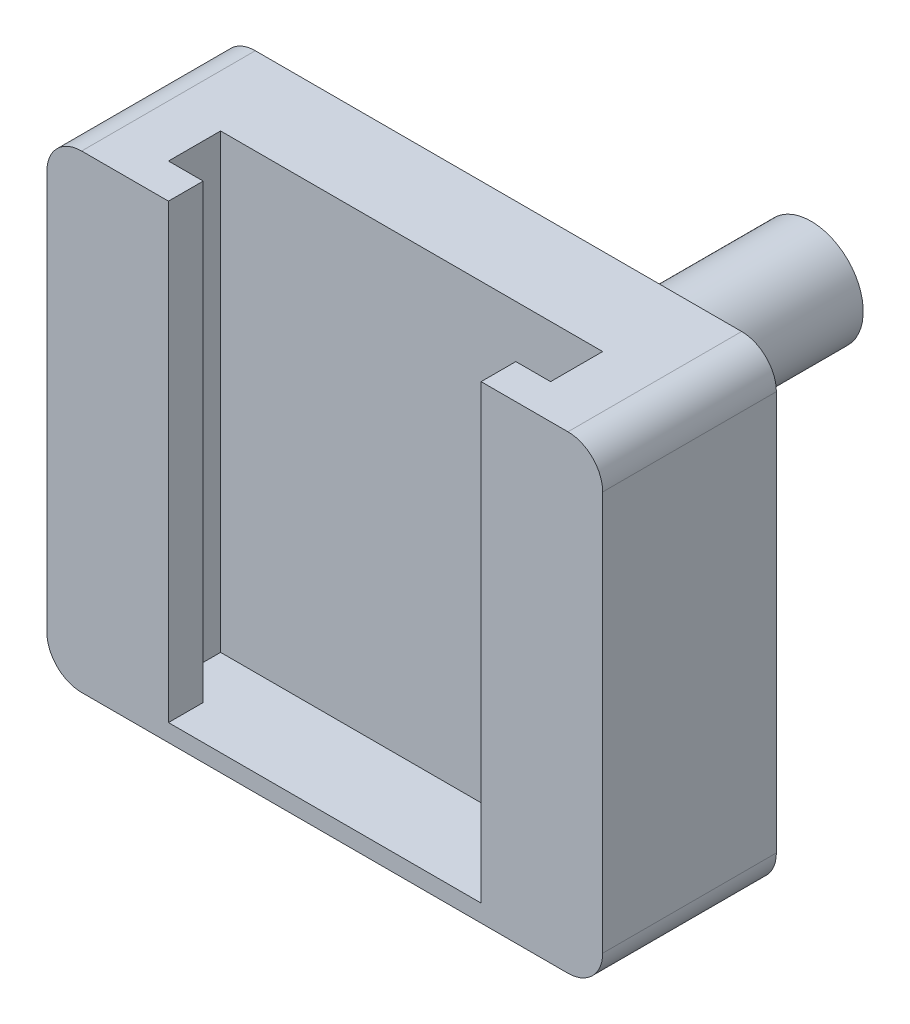
SolidWorks part; units mm, degrees
ref_plane "Front Plane" through (0, 0, 0) normal (0, 0, 1) x (1, 0, 0)
ref_plane "Top Plane" through (0, 0, 0) normal (0, 1, 0) x (1, 0, 0)
ref_plane "Right Plane" through (0, 0, 0) normal (1, 0, 0) x (0, 0, -1)
sketch "Sketch1" plane through (0, 0, 0) normal (0, 0, 1) x (1, 0, 0)
  line L1 (-16, -13.5) -> (16, -13.5)
  line L2 (-16, -13.5) -> (-16, 13.5)
  line L3 (-16, 13.5) -> (16, 13.5)
  line L4 (16, -13.5) -> (16, 13.5)
  line L5 (-16, -13.5) -> (16, 13.5) construction
  line L6 (-16, 13.5) -> (16, -13.5) construction
  point P0 (0, 0)
  dimension "D1" = 32
  dimension "D2" = 27
extrude "Boss-Extrude1" add sketch "Sketch1" along normal blind 10 contours L3 L4 L1 L2
fillet "Fillet1" radius 2 4 edges at (16, 13.5, 5) (-16, 13.5, 5) (16, -13.5, 5) (-16, -13.5, 5)
sketch "Sketch2" plane through (0, 13.5, 0) normal (0, 1, 0) x (1, 0, 0)
  line L0 (-9, -10) -> (-9, -8)
  line L1 (-14, -10) -> (14, -10) construction
  line L2 (-9, -8) -> (-11, -8)
  line L3 (-11, -8) -> (-11, -5)
  line L4 (-11, -5) -> (11, -5)
  line L5 (11, -5) -> (11, -8)
  line L6 (11, -8) -> (9, -8)
  line L7 (9, -8) -> (9, -10)
  line L8 (0, 0) -> (0, -10) construction
  line L9 (-14, 0) -> (14, 0) construction
  line L10 (-9, -10) -> (9, -10)
  point P15 (0, -5)
  dimension "D1" = 22
  dimension "D2" = 2
  dimension "D3" = 3
  dimension "D4" = 18
extrude "Cut-Extrude4" cut sketch "Sketch2" against normal offset from surface (26 mm away) 1 up to face at (0, -13.5, 5)
sketch "Sketch4" plane through (0, 0, 0) normal (0, 0, -1) x (-1, 0, 0)
  line L0 (-15.4142, 12.9142) -> (15.4142, -12.9142) construction
  line L1 (15.4142, -12.9142) -> (-15.4142, -12.9142) construction
  line L2 (-15.4142, -12.9142) -> (15.4142, 12.9142) construction
  arc A0 (-14, 13.5) -> (-16, 11.5) centre (-14, 11.5) ccw construction
  arc A1 (14, -13.5) -> (16, -11.5) centre (14, -11.5) ccw construction
  arc A2 (-16, -11.5) -> (-14, -13.5) centre (-14, -11.5) ccw construction
  arc A3 (16, 11.5) -> (14, 13.5) centre (14, 11.5) ccw construction
  circle A4 centre (0, 0) radius 3
  dimension "D1" = 6
extrude "Boss-Extrude2" add sketch "Sketch4" along normal blind 18
fillet "Fillet2" radius 2 1 edges at (-3, 0, 0)
